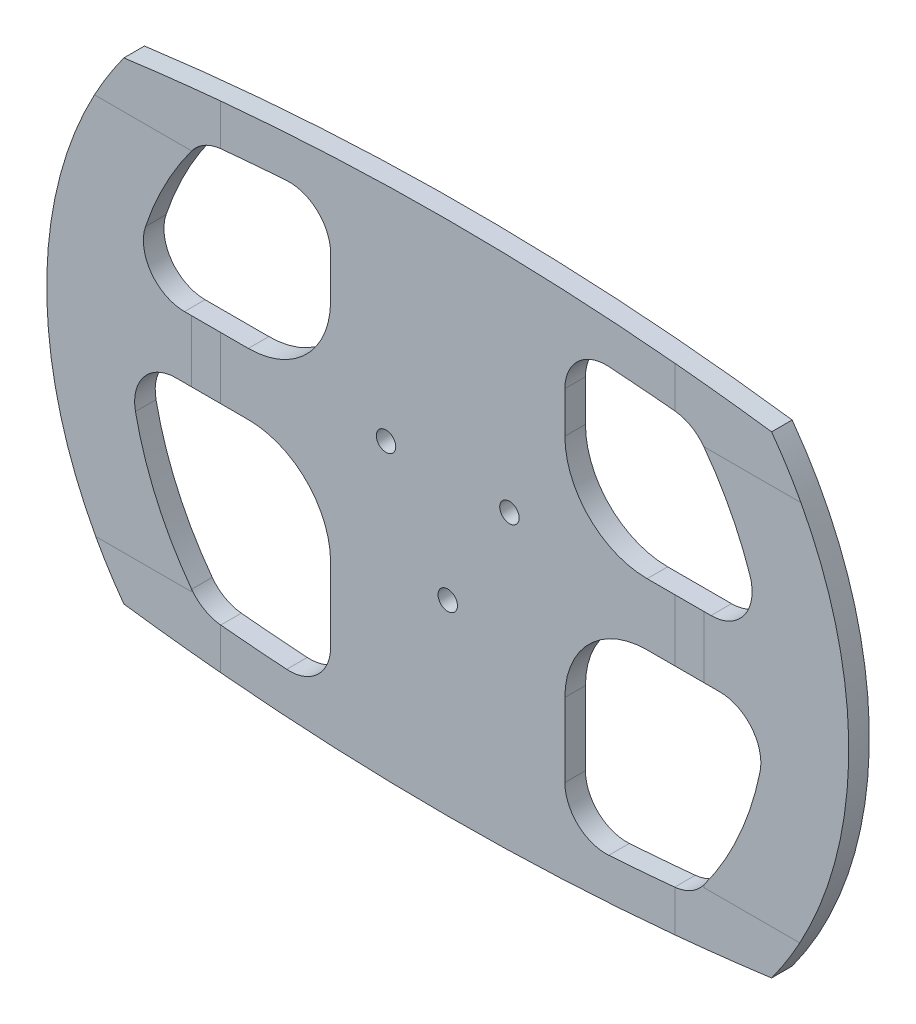
SolidWorks part; units mm, degrees
material "Hexcel AS4C (3000 Filaments)"
ref_plane "Front Plane" through (0, 0, 0) normal (0, 0, 1) x (1, 0, 0)
ref_plane "Top Plane" through (0, 0, 0) normal (0, 1, 0) x (1, 0, 0)
ref_plane "Right Plane" through (0, 0, 0) normal (1, 0, 0) x (0, 0, -1)
sketch "Sketch2" plane through (0, 0, 0) normal (0, 0, 1) x (1, 0, 0)
  line L0 (-81.0894, 75.3249) -> (-81.0894, -75.3249)
  line L1 (81.0894, 75.3249) -> (81.0894, -75.3249)
  arc A0 (-100, 73.0249) -> (100, 73.0249) centre (0, -670.2786) cw
  arc A1 (-100, -73.0249) -> (100, -73.0249) centre (0, 670.2786) ccw
  arc A2 (-100, 73.0249) -> (-100, -73.0249) centre (0, 0) ccw
  arc A3 (100, 73.0249) -> (100, -73.0249) centre (0, 0) cw
  dimension "D2" = 123.825
  dimension "D3" = 123.825
  dimension "D1" = 750
  dimension "D4" = 750
  dimension "D8" = 200
  dimension "D5" = 247.65
  dimension "D6" = 19.05
  dimension "D7" = 19.05
extrude "Boss-Extrude1" add sketch "Sketch2" along normal blind 6.35 contours A0 A3 A1 A2
sketch "Sketch3" plane through (0, 0, 6.35) normal (0, 0, 1) x (1, 0, 0)
  line L0 (0, 78.018) -> (0, -83.804) construction
  line L1 (-61.5728, 14.5424) -> (-81.2811, 14.5424)
  line L2 (-36.1728, 39.9424) -> (-36.1728, 52.6714)
  line L3 (36.1728, -29.9076) -> (36.1728, -52.6714)
  line L4 (61.5728, -4.5076) -> (83.9802, -4.5076)
  line L5 (-61.5728, -4.5076) -> (-83.9802, -4.5076)
  line L6 (-36.1728, -29.9076) -> (-36.1728, -52.6714)
  line L7 (36.1728, 39.9424) -> (36.1728, 52.6714)
  line L8 (61.5728, 14.5424) -> (81.2811, 14.5424)
  arc A0 (-70.0811, 63.6832) -> (-49.7294, 65.3424) centre (0, -670.2786) cw
  arc A1 (-79.0775, 58.6023) -> (-93.3228, 31.2784) centre (0, 0) ccw
  arc A2 (-100, 73.0249) -> (-100, -73.0249) centre (0, 0) ccw construction
  arc A3 (-96.4217, -19.7568) -> (-79.0775, -58.6023) centre (0, 0) ccw
  arc A4 (-70.0811, -63.6832) -> (-49.7294, -65.3424) centre (0, 670.2786) ccw
  arc A7 (-100, -73.0249) -> (100, -73.0249) centre (0, 670.2786) ccw construction
  arc A8 (-70.0811, -63.6832) -> (-79.0775, -58.6023) centre (-68.8739, -51.0407) cw
  arc A9 (-49.7294, -65.3424) -> (-36.1728, -52.6714) centre (-48.8728, -52.6714) ccw
  arc A10 (-36.1728, -29.9076) -> (-61.5728, -4.5076) centre (-61.5728, -29.9076) ccw
  arc A11 (-96.4217, -19.7568) -> (-83.9802, -4.5076) centre (-83.9802, -17.2076) cw
  arc A12 (-36.1728, 52.6714) -> (-49.7294, 65.3424) centre (-48.8728, 52.6714) ccw
  arc A13 (-61.5728, 14.5424) -> (-36.1728, 39.9424) centre (-61.5728, 39.9424) ccw
  arc A14 (-81.2811, 14.5424) -> (-93.3228, 31.2784) centre (-81.2811, 27.2424) cw
  arc A15 (-70.0811, 63.6832) -> (-79.0775, 58.6023) centre (-68.8739, 51.0407) ccw
  arc A16 (100, 73.0249) -> (-100, 73.0249) centre (0, -670.2786) ccw construction
  arc A17 (81.2811, 14.5424) -> (93.3228, 31.2784) centre (81.2811, 27.2424) ccw
  arc A18 (96.4217, -19.7568) -> (83.9802, -4.5076) centre (83.9802, -17.2076) ccw
  arc A19 (96.4217, -19.7568) -> (79.0775, -58.6023) centre (0, 0) cw
  arc A20 (79.0775, 58.6023) -> (93.3228, 31.2784) centre (0, 0) cw
  arc A21 (70.0811, 63.6832) -> (79.0775, 58.6023) centre (68.8739, 51.0407) cw
  arc A22 (61.5728, 14.5424) -> (36.1728, 39.9424) centre (61.5728, 39.9424) cw
  arc A23 (36.1728, 52.6714) -> (49.7294, 65.3424) centre (48.8728, 52.6714) cw
  arc A24 (36.1728, -29.9076) -> (61.5728, -4.5076) centre (61.5728, -29.9076) cw
  arc A25 (49.7294, -65.3424) -> (36.1728, -52.6714) centre (48.8728, -52.6714) cw
  arc A26 (70.0811, -63.6832) -> (79.0775, -58.6023) centre (68.8739, -51.0407) ccw
  arc A27 (70.0811, -63.6832) -> (49.7294, -65.3424) centre (0, 670.2786) cw
  arc A28 (70.0811, 63.6832) -> (49.7294, 65.3424) centre (0, -670.2786) ccw
  dimension "D1" = 50.8
  dimension "D2" = 12.7
  dimension "D4" = 25.4
  dimension "D5" = 12.7
  dimension "D6" = 25.4
  dimension "D7" = 12.7
  dimension "D9" = 12.7
  dimension "D10" = 25.4
  dimension "D11" = 25.4
  dimension "D12" = 12.7
  dimension "D3" = 57.15
  dimension "D8" = 19.05
extrude "Cut-Extrude1" cut sketch "Sketch3" against normal through all
sketch "Sketch4" plane through (0, 0, 6.35) normal (0, 0, 1) x (1, 0, 0)
  line L1 (0, -21.997) -> (19.05, 10.9985) construction
  line L2 (19.05, 10.9985) -> (-19.05, 10.9985) construction
  line L3 (-19.05, 10.9985) -> (0, -21.997) construction
  circle A0 centre (0, 0) radius 10.9985 construction
  circle A1 centre (-19.05, 10.9985) radius 3
  circle A2 centre (19.05, 10.9985) radius 3
  circle A3 centre (0, -21.997) radius 3
  dimension "D3" = 6
  dimension "D4" = 6
  dimension "D5" = 6
  dimension "D1" = 38.1
  dimension "D2" = 19.05
extrude "Cut-Extrude2" cut sketch "Sketch4" against normal through all
sketch "Sketch5" plane through (0, 0, 0) normal (0, 0, 1) x (1, 0, 0)
  line L1 (-70.2172, 112.6453) -> (-137.8784, 112.6453)
  line L2 (-70.2172, 112.6453) -> (-70.2172, -113.3762)
  line L3 (-70.2172, -113.3762) -> (-137.8784, -113.3762)
  line L4 (-137.8784, 112.6453) -> (-137.8784, -113.3762)
  line L5 (70.2172, 104.918) -> (139.0946, 104.918)
  line L6 (70.2172, 104.918) -> (70.2172, -113.3762)
  line L7 (70.2172, -113.3762) -> (139.0946, -113.3762)
  line L8 (139.0946, 104.918) -> (139.0946, -113.3762)
split line "Split Line1"
sketch "Sketch6" plane through (0, 0, 6.35) normal (0, 0, 1) x (1, 0, 0)
  line L1 (-79.0775, 58.6023) -> (-140.4343, 58.6023)
  line L2 (-79.0775, 58.6023) -> (-79.0775, -59.3009)
  line L3 (-79.0775, -59.3009) -> (-140.4343, -59.3009)
  line L4 (-140.4343, 58.6023) -> (-140.4343, -59.3009)
  line L5 (79.0775, 58.6023) -> (138.9971, 58.6023)
  line L6 (79.0775, 58.6023) -> (79.0775, -59.3009)
  line L7 (79.0775, -59.3009) -> (138.9971, -59.3009)
  line L8 (138.9971, 58.6023) -> (138.9971, -59.3009)
split line "Split Line2"
